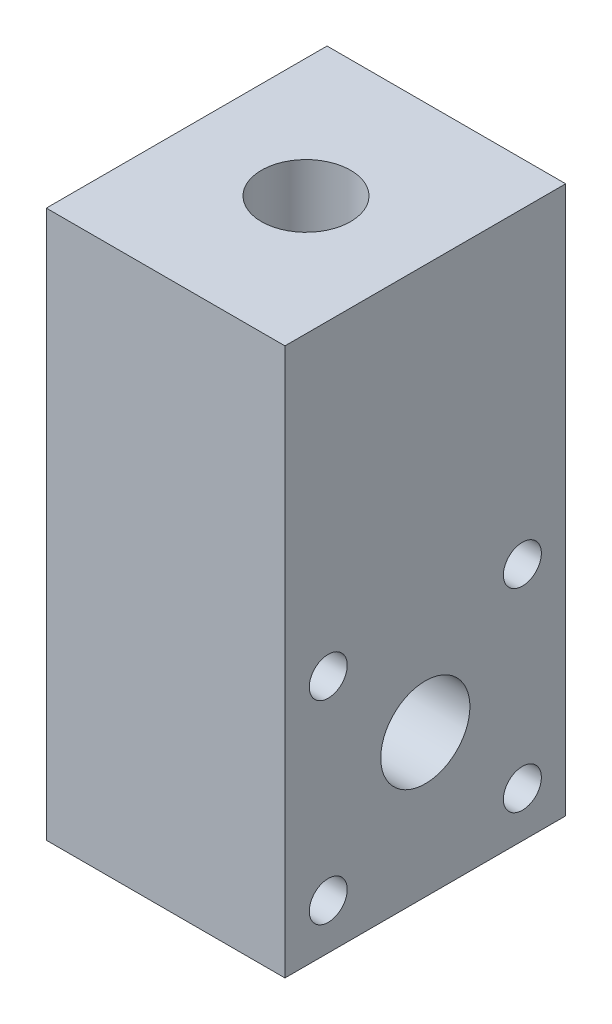
SolidWorks part; units mm, degrees
material "ABS"
ref_plane "Plan de face" through (0, 0, 0) normal (0, 0, 1) x (1, 0, 0)
ref_plane "Plan de dessus" through (0, 0, 0) normal (0, 1, 0) x (1, 0, 0)
ref_plane "Plan de droite" through (0, 0, 0) normal (1, 0, 0) x (0, 0, -1)
sketch "Esquisse1" plane through (0, 0, 0) normal (0, 1, 0) x (1, 0, 0)
  line L1 (-8.5, -10) -> (8.5, -10)
  line L2 (-8.5, -10) -> (-8.5, 10)
  line L3 (-8.5, 10) -> (8.5, 10)
  line L4 (8.5, -10) -> (8.5, 10)
  line L5 (-8.5, -10) -> (8.5, 10) construction
  line L6 (-8.5, 10) -> (8.5, -10) construction
  point P0 (0, 0)
  dimension "D1" = 17
  dimension "D2" = 20
extrude "Boss.-Extru.1" add sketch "Esquisse1" along normal mid plane 39
sketch "Esquisse2" plane through (-8.5, 0, 0) normal (-1, 0, 0) x (0, 0, 1)
  line L0 (-10, -19.5) -> (10, -19.5) construction
  circle A0 centre (0, -9.34) radius 3.175
  dimension "D1" = 6.35
  dimension "D2" = 10.16
extrude "Enlèv. mat.-Extru.1" cut sketch "Esquisse2" against normal through all
sketch "Esquisse3" plane through (0, 19.5, 0) normal (0, 1, 0) x (1, 0, 0)
  circle A0 centre (0, 0) radius 3.175
  dimension "D1" = 6.35
extrude "Enlèv. mat.-Extru.2" cut sketch "Esquisse3" against normal blind 12.7
sketch "Esquisse4" plane through (8.5, 0, 0) normal (1, 0, 0) x (0, 0, -1)
  circle A0 centre (-6.9148, -2.4252) radius 1.3525
  circle A1 centre (6.9148, -2.4252) radius 1.3525
  circle A2 centre (-6.9148, -16.2548) radius 1.3525
  circle A3 centre (6.9148, -16.2548) radius 1.3525
extrude "Enlèv. mat.-Extru.3" cut sketch "Esquisse4" against normal through all
